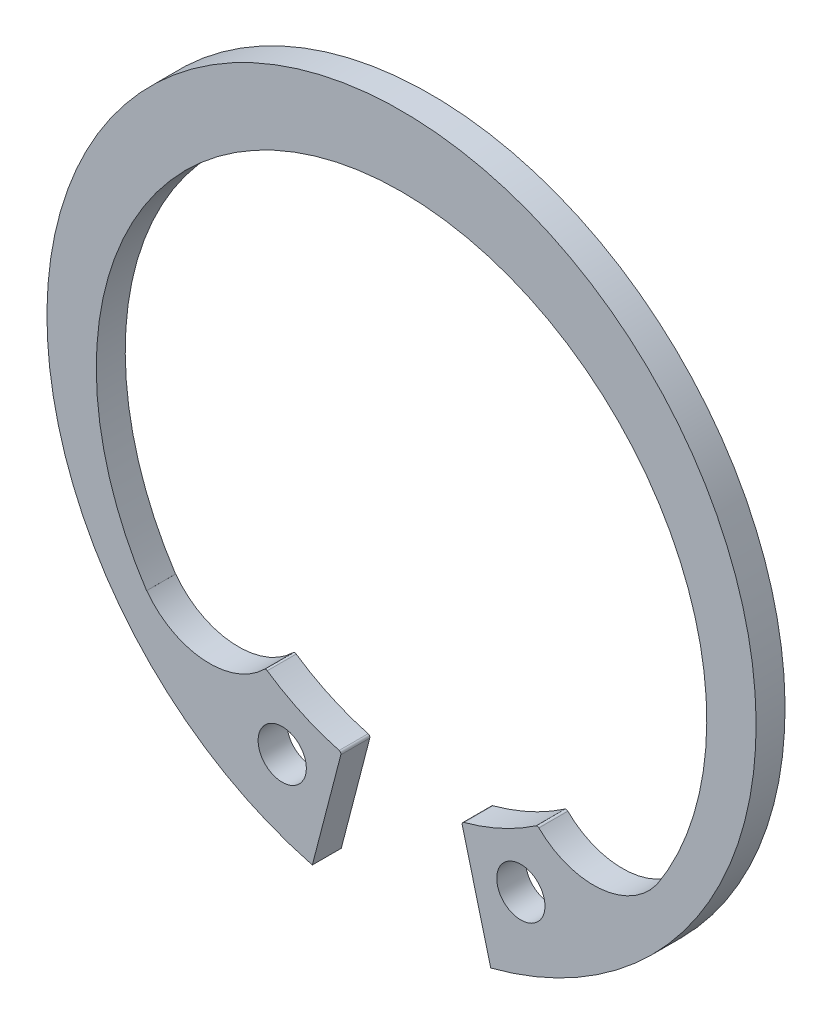
SolidWorks part; units mm, degrees
extrude "Body" add sketch "BodySke" against normal blind 1.2
sketch "BodySke" plane through (0, 0, 0) normal (0, 0, 1) x (1, 0, 0)
  line L0 (-1.5431, 0) -> (1.5431, 0) construction
  line L1 (0, 0) -> (0, 11.8) construction
  line L2 (3.6983, -14.2272) -> (2.9619, -11.3942)
  line L3 (-3.6983, -14.2272) -> (-2.9619, -11.3942)
  line L4 (0, 0) -> (10.306, -10.4822) construction
  line L5 (0, 0) -> (-10.306, -10.4822) construction
  line L6 (-4.6944, -9.9106) -> (-5.1975, -11.8463) construction
  line L7 (4.7571, -10.152) -> (5.1348, -11.6049) construction
  arc A0 (-2.9619, -11.3942) -> (-6.3981, -9.4314) centre (-4.946, -10.8784) ccw
  arc A1 (6.3981, -9.4314) -> (2.9619, -11.3942) centre (4.946, -10.8784) ccw
  arc A2 (9.2894, -9.4482) -> (-9.2894, -9.4482) centre (0, -0.8547) ccw construction
  arc A3 (3.6983, -14.2272) -> (-3.6983, -14.2272) centre (0, 0) ccw
  circle A4 centre (4.946, -10.8784) radius 1
  circle A5 centre (-4.946, -10.8784) radius 1
  circle A6 centre (4.946, -10.8784) radius 2.05 construction
  arc A7 (9.3678, -9.3627) -> (-9.3678, -9.3627) centre (0, -0.8547) ccw
  arc A8 (-4.946, -10.8784) -> (4.946, -10.8784) centre (0, 0) ccw construction
  arc A9 (-9.3678, -9.3627) -> (-6.3981, -9.4314) centre (-7.8503, -7.9845) ccw
  arc A10 (6.3981, -9.4314) -> (9.3678, -9.3627) centre (7.8503, -7.9845) ccw
  dimension "HoleDia" = 2
  dimension "HoleOffsetRad" = 11.95
  dimension "GrooveDia" = 29.4
  dimension "TipRad" = 2.05
  dimension "FilletRad" = 2.05
  dimension "LargeRad" = 11.8
  dimension "SmallRad" = 13.25
  dimension "SmallAngle" = 89.029
  dimension "GapAngle" = 29.143
ref_plane "Plane1" through (0, 0, 0) normal (0, 0, 1) x (1, 0, 0)
ref_plane "Plane2" through (0, 0, 0) normal (0, 1, 0) x (1, 0, 0)
ref_plane "Plane3" through (0, 0, 0) normal (1, 0, 0) x (0, 0, -1)
sketch "Clipboard" plane through (0, 0, 0) normal (0, 0, 1) x (1, 0, 0)
  line L0 (0, 0) -> (2.9, 0)
  line L1 (0, 0) -> (0, 1.45)
  line L2 (0, 0) -> (0, -4.8)
  circle A0 centre (0, 0) radius 1
  circle A1 centre (0, 0) radius 14
  dimension "HoleDia" = 2
  dimension "BoreDia" = 28
  dimension "LargeSection" = 2.9
  dimension "SmallSection" = 1.45
  dimension "LugSection" = 4.8
sketch "ModLugSke" plane through (0, 0, 0) normal (0, 0, 1) x (1, 0, 0)
  line L0 (3.6983, -14.2272) -> (2.5157, -9.6779)
  line L1 (-3.6983, -14.2272) -> (-2.5157, -9.6779)
  line L2 (7.9601, -5.8862) -> (11.8195, -8.74) construction
  line L3 (-7.9601, -5.8862) -> (-11.8195, -8.74) construction
  line L4 (-3.6983, -14.2272) -> (-2.9619, -11.3942) construction
  line L5 (2.9619, -11.3942) -> (3.6983, -14.2272) construction
  line L6 (0, 0) -> (0, -18.0732) construction
  line L7 (10.5634, -7.8112) -> (11.8195, -8.74)
  line L8 (-11.8195, -8.74) -> (-10.5634, -7.8112)
  arc A0 (3.6983, -14.2272) -> (11.8195, -8.74) centre (0, 0) ccw
  arc A1 (-5.5669, -8.1866) -> (-2.5864, -9.5562) centre (0, 0) ccw
  arc A2 (3.6983, -14.2272) -> (-3.6983, -14.2272) centre (0, 0) ccw construction
  arc A3 (6.3981, -9.4314) -> (2.9619, -11.3942) centre (4.946, -10.8784) ccw construction
  arc A4 (-5.5669, -8.1866) -> (-5.6931, -8.1979) centre (-5.6231, -8.2693) ccw
  arc A5 (-10.5634, -7.8112) -> (-5.6931, -8.1979) centre (-7.9601, -5.8862) ccw
  arc A6 (9.3678, -9.3627) -> (-9.3678, -9.3627) centre (0, -0.8547) ccw construction
  arc A7 (5.6931, -8.1979) -> (10.5634, -7.8112) centre (7.9601, -5.8862) ccw
  arc A8 (2.5864, -9.5562) -> (5.5669, -8.1866) centre (0, 0) ccw
  arc A9 (-11.8195, -8.74) -> (-3.6983, -14.2272) centre (0, 0) ccw
  circle A10 centre (-4.946, -10.8784) radius 1
  circle A11 centre (-4.946, -10.8784) radius 1 construction
  circle A12 centre (4.946, -10.8784) radius 1
  circle A13 centre (4.946, -10.8784) radius 1 construction
  arc A14 (-2.5864, -9.5562) -> (-2.5157, -9.6779) centre (-2.6125, -9.6527) cw
  arc A15 (2.5864, -9.5562) -> (2.5157, -9.6779) centre (2.6125, -9.6527) ccw
  arc A16 (5.5669, -8.1866) -> (5.6931, -8.1979) centre (5.6231, -8.2693) cw
  point P43 (2.4907, -9.5816)
  dimension "D1" = 0.1
extrude "ModLug" add sketch "ModLugSke" against normal through all
sketch "UnlSke" [suppressed] plane through (0, 0, 0) normal (0, 0, 1) x (1, 0, 0)
  line L0 (2.1178, -8.3352) -> (3.2259, -12.6966)
  line L1 (-2.1178, -8.3352) -> (-3.2259, -12.6966)
  line L2 (-3.2259, -12.6966) -> (-2.1422, -8.4315) construction
  line L3 (2.1422, -8.4315) -> (3.2259, -12.6966) construction
  arc A0 (2.1178, -8.3352) -> (-2.1178, -8.3352) centre (0, 0) ccw
  arc A1 (3.2259, -12.6966) -> (-3.2259, -12.6966) centre (0, 0) ccw
  arc A2 (3.2259, -12.6966) -> (-3.2259, -12.6966) centre (0, 0) ccw construction
  circle A4 centre (-4.4431, -9.5688) radius 1
  circle A5 centre (4.4431, -9.5688) radius 1
  circle A6 centre (4.4431, -9.5688) radius 1 construction
  circle A7 centre (-4.4431, -9.5688) radius 1 construction
  arc A8 (2.2134, -8.3103) -> (4.9183, -7.0548) centre (0, 0) ccw construction
extrude "Unlug" [suppressed] add sketch "UnlSke" against normal through all
equation "' \"BoreDia@Clipboard\" = 8"
equation "' \"Thickness@Body\" = 0.8"
equation "' \"GrooveDia@BodySke\" = 8.4"
equation "' \"LugSection@Clipboard\" = 2.4"
equation "' \"LargeSection@Clipboard\" = 1.1"
equation "' \"HoleDia@Clipboard\" = 1.0"
equation "' \"BoreDia@Clipboard\" = 25"
equation "' \"Thickness@Body\" = 1.2"
equation "' \"GrooveDia@BodySke\" = 26.2"
equation "' \"LugSection@Clipboard\" = 4.5"
equation "' \"LargeSection@Clipboard\" = 2.7"
equation "' \"HoleDia@Clipboard\" = 2"
equation "\"SmallSection@Clipboard\" = \"LargeSection@Clipboard\" * 0.5"
equation "\"TipRad@BodySke\" = (\"LugSection@Clipboard\" - (\"GrooveDia@BodySke\" / 2  -  \"BoreDia@Clipboard\" / 2 ) ) / 2"
equation "\"HoleOffsetRad@BodySke\" = (\"GrooveDia@BodySke\" / 2) - \"LugSection@Clipboard\"  + \"TipRad@BodySke\""
equation "\"LargeRad@BodySke\" =  \"GrooveDia@BodySke\" / 2 -  \"LargeSection@Clipboard\""
equation "\"SmallRad@BodySke\" =  \"GrooveDia@BodySke\" / 2 -  \"SmallSection@Clipboard\""
equation "\"HoleDia@BodySke\" =  \"HoleDia@Clipboard\""
equation "\"FilletRad@BodySke\" = \"TipRad@BodySke\" * 1.0"
equation "\"GapAngle@BodySke\" = 360 - 0.965 * 360 * ( \"BoreDia@Clipboard\" /  \"GrooveDia@BodySke\")"
equation "\"LugAng@ModLugSke\" = \"GapAngle@BodySke\"  + 2 * 360 * (\"LugSection@Clipboard\" / (\"BoreDia@Clipboard\" * 3.1416))"
